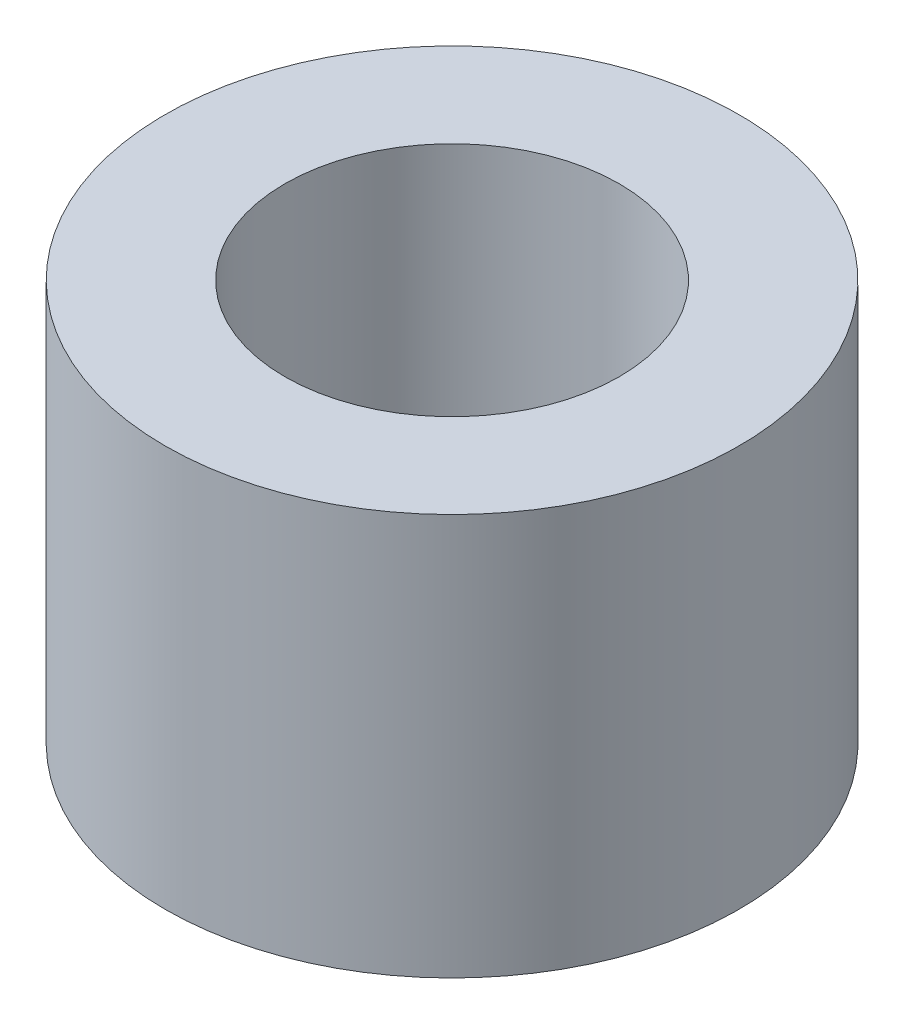
SolidWorks part; units mm, degrees
ref_plane "Top Plane" through (0, 0, 0) normal (0, 0, 1) x (1, 0, 0)
ref_plane "Front Plane" through (0, 0, 0) normal (0, 1, 0) x (1, 0, 0)
ref_plane "Right Plane" through (0, 0, 0) normal (1, 0, 0) x (0, 0, -1)
sketch "Profile Sketch" plane through (0, 0, 0) normal (0, 1, 0) x (1, 0, 0)
  circle A0 centre (0, 0) radius 4.1656
  circle A1 centre (0, 0) radius 7.1501
  dimension "D1" = 8.3312
  dimension "D2" = 14.3002
extrude "Profile Extrude" add sketch "Profile Sketch" along normal blind 10
